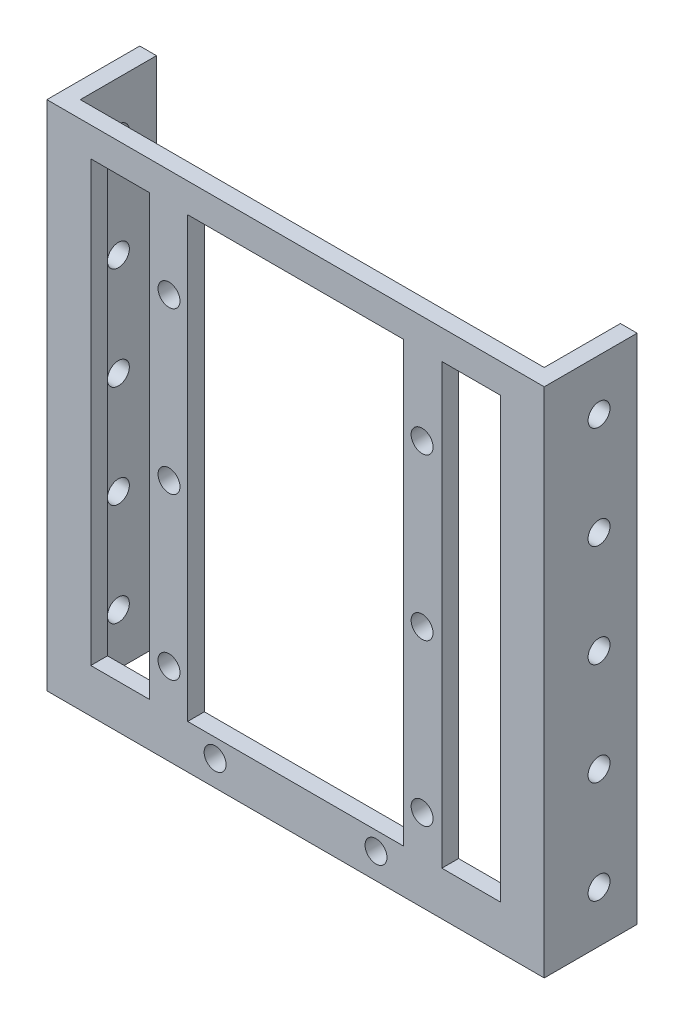
SolidWorks part; units mm, degrees
material "7075-O (SS)"
ref_plane "Front Plane" through (0, 0, 0) normal (0, 0, 1) x (1, 0, 0)
ref_plane "Top Plane" through (0, 0, 0) normal (0, 1, 0) x (1, 0, 0)
ref_plane "Right Plane" through (0, 0, 0) normal (1, 0, 0) x (0, 0, -1)
sketch "Sketch1" plane through (0, 0, 0) normal (0, 0, 1) x (1, 0, 0)
  line L0 (0, 0) -> (0, 74.3422) construction
  line L1 (20.75, 70) -> (-20.75, 70)
  line L2 (-20.75, 70) -> (-20.75, 0)
  line L3 (-20.75, 0) -> (20.75, 0)
  line L4 (14.75, 66) -> (14.75, 6)
  line L5 (-14.75, 66) -> (14.75, 66)
  line L6 (-14.75, 66) -> (-14.75, 6)
  line L7 (-14.75, 6) -> (14.75, 6)
  line L9 (20.75, 70) -> (20.75, 0)
  circle A0 centre (-17.3, 11.25) radius 1.5
  circle A1 centre (-11, 3.5) radius 1.5
  circle A2 centre (-17.3, 33.25) radius 1.5
  circle A3 centre (-17.3, 55.25) radius 1.5
  circle A4 centre (17.3, 55.25) radius 1.5
  circle A5 centre (17.3, 33.25) radius 1.5
  circle A6 centre (11, 3.5) radius 1.5
  circle A7 centre (17.3, 11.25) radius 1.5
  point P34 (0, 6)
  point P35 (0, 66)
  point P37 (0, 70)
  dimension "D5" = 3
  dimension "D6" = 3
  dimension "D9" = 3
  dimension "D10" = 3
  dimension "D1" = 6
  dimension "D2" = 6
  dimension "D3" = 60
  dimension "D4" = 4
  dimension "D7" = 10.75
  dimension "D8" = 34.6
  dimension "D11" = 22
  dimension "D12" = 22
  dimension "D13" = 22
  dimension "D14" = 29.5
  dimension "D15" = 2.5
extrude "Boss-Extrude1" add sketch "Sketch1" along normal mid plane 2.286
sketch "Sketch2" plane through (0, 0, 1.143) normal (0, 0, 1) x (1, 0, 0)
  line L0 (0, 0) -> (0, 87.2499) construction
  line L1 (-20.75, 0) -> (-34, 0)
  line L2 (-20.75, 0) -> (-20.75, 70)
  line L3 (-20.75, 70) -> (-34, 70)
  line L4 (-34, 0) -> (-34, 70)
  line L5 (20.75, 70) -> (-20.75, 70) construction
  dimension "D1" = 68
extrude "Boss-Extrude2" add sketch "Sketch2" against normal blind 2.286
mirror "Mirror4" about plane through (0, 0, 0) normal (1, 0, 0) of "Boss-Extrude2"
sketch "Sketch8" plane through (0, 0, 1.143) normal (0, 0, 1) x (1, 0, 0)
  line L0 (0, 0) -> (0, 47.278) construction
  line L1 (14.75, 66) -> (-14.75, 66) construction
  line L2 (-28, 66) -> (-20, 66)
  line L3 (-28, 66) -> (-28, 6)
  line L4 (-28, 6) -> (-20, 6)
  line L5 (-20, 66) -> (-20, 6)
  line L6 (-14.75, 6) -> (14.75, 6) construction
  dimension "D1" = 20
  dimension "D2" = 8
extrude "Cut-Extrude1" cut sketch "Sketch8" against normal blind 10
mirror "Mirror3" about plane through (0, 0, 0) normal (1, 0, 0) of "Cut-Extrude1"
sketch "Sketch9" plane through (0, 0, -1.143) normal (0, 0, -1) x (-1, 0, 0)
  line L0 (-34, 70) -> (34, 70) construction
  line L1 (34, 0) -> (31.714, 0)
  line L2 (34, 0) -> (34, 70)
  line L3 (34, 70) -> (31.714, 70)
  line L4 (31.714, 0) -> (31.714, 70)
  dimension "D1" = 2.286
extrude "Boss-Extrude3" add sketch "Sketch9" along normal blind 10.414
mirror "Mirror5" about plane through (0, 0, 0) normal (1, 0, 0) of "Boss-Extrude3"
sketch "Sketch10" plane through (-34, 0, 0) normal (-1, 0, 0) x (0, 0, 1)
  line L0 (1.143, 35) -> (-35.1074, 35) construction
  line L1 (1.143, 70) -> (1.143, 0) construction
  line L2 (-6.35, 35) -> (-6.35, 13.5449) construction
  point P4 (-6.35, 35)
  point P7 (-6.35, 21)
  point P8 (-6.35, 7)
  point P9 (-6.35, 63)
  point P10 (-6.35, 49)
  dimension "D1" = 7.493
  dimension "D2" = 28
  dimension "D3" = 28
  dimension "D4" = 28
  dimension "D5" = 14
hole_wizard "Ø3.0mm Dowel Hole1" positions "Sketch11" profile "Sketch12" hole size "Ø3.0" standard "ISO" end condition through all
sketch "Sketch11" plane through (-34, 0, 0) normal (-1, 0, 0) x (0, 0, 1)
  point P0 (-6.35, 35)
  point P3 (-6.35, 21)
  point P7 (-6.35, 49)
  point P10 (-6.35, 63)
  point P18 (-6.35, 7)
sketch "Sketch12" plane through (-34, 35, -6.35) normal (0, 1, 0) x (0, 0, 1)
  line L0 (0, 0) -> (0, 68)
  line L1 (0, 68) -> (1.5, 68)
  line L2 (1.5, 68) -> (1.5, 0)
  line L5 (1.5, 0) -> (0, 0)
  line L11 (0, -6.35) -> (0, 107.95) construction
  dimension "Thru Hole Dia." = 3
  dimension "Thru Hole Depth" = 68
